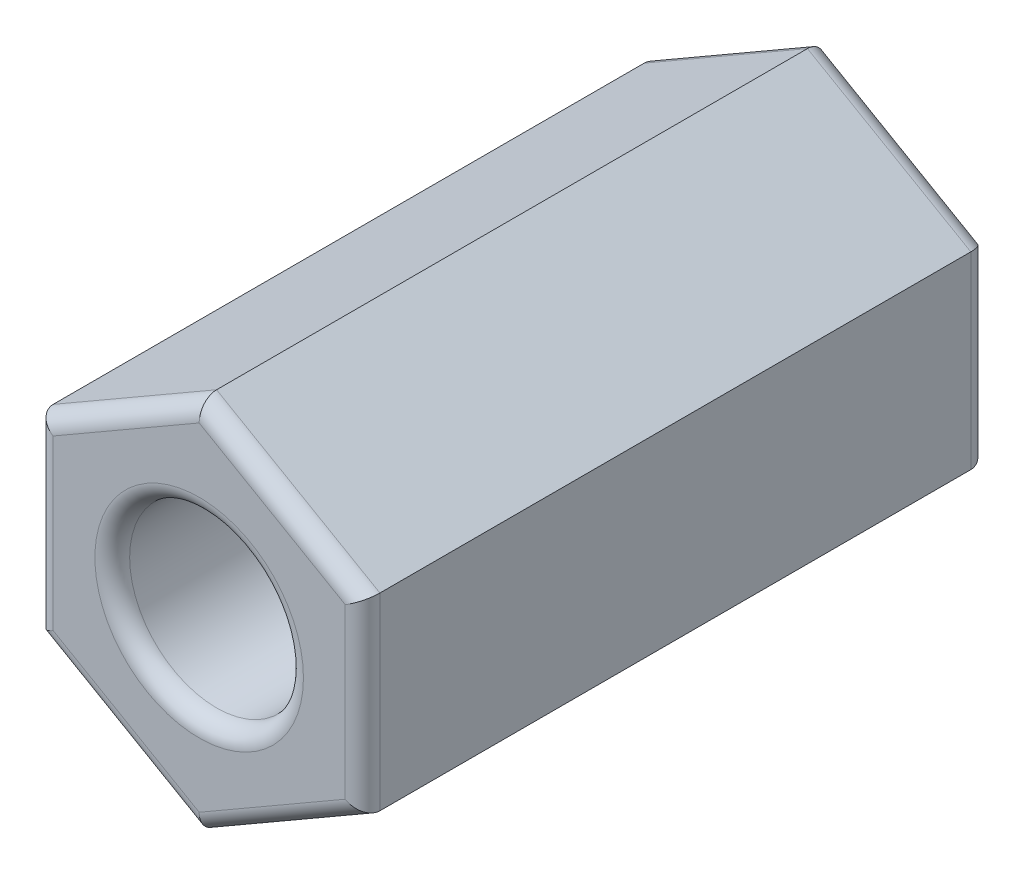
SolidWorks part; units mm, degrees
ref_plane "Alzado" through (0, 0, 0) normal (0, 0, 1) x (1, 0, 0)
ref_plane "Planta" through (0, 0, 0) normal (0, 1, 0) x (1, 0, 0)
ref_plane "Vista lateral" through (0, 0, 0) normal (1, 0, 0) x (0, 0, -1)
sketch "Croquis1" plane through (0, 0, 0) normal (0, 0, 1) x (1, 0, 0)
  line L1 (2.35, 1.3568) -> (0, 2.7135)
  line L2 (0, 2.7135) -> (-2.35, 1.3568)
  line L3 (-2.35, 1.3568) -> (-2.35, -1.3568)
  line L4 (-2.35, -1.3568) -> (0, -2.7135)
  line L5 (0, -2.7135) -> (2.35, -1.3568)
  line L6 (2.35, -1.3568) -> (2.35, 1.3568)
  circle A0 centre (0, 0) radius 2.35 construction
  circle A1 centre (0, 0) radius 1.25
  dimension "D2" = 2.5
  dimension "D1" = 4.7
extrude "Saliente-Extruir1" add sketch "Croquis1" along normal blind 9
fillet "Redondeo1" radius 0.25 12 edges at (-2.35, 0, 0) (-2.35, 0, 9) (-1.175, -2.0352, 0) (-1.175, -2.0352, 9) (1.175, -2.0352, 0) (1.175, -2.0352, 9) (2.35, 0, 9) (2.35, 0, 0) (-1.175, 2.0352, 0) (-1.175, 2.0352, 9) (1.175, 2.0352, 9) (1.175, 2.0352, 0)
fillet "Redondeo2" radius 0.25 2 edges at (1.25, 0, 0) (1.25, 0, 9)
